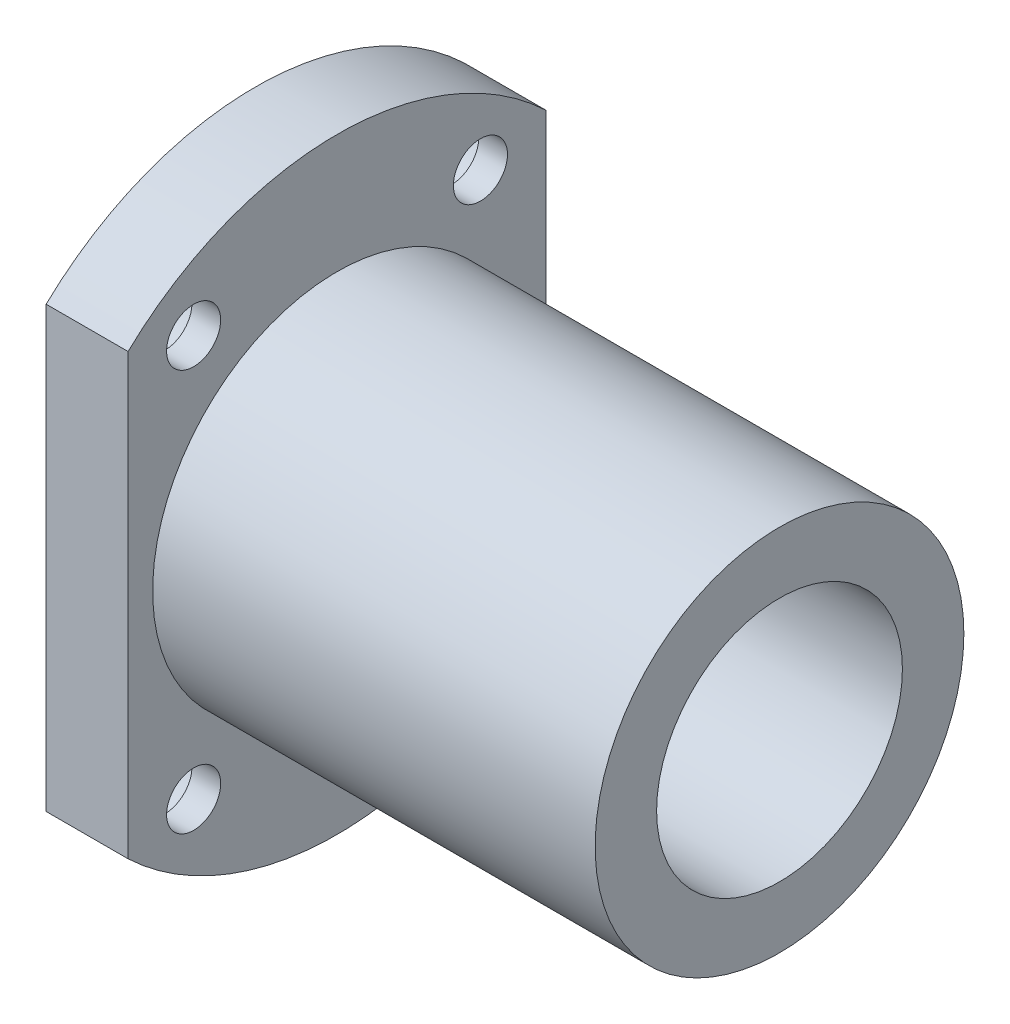
SolidWorks part; units mm, degrees
material "AISI 1045 钢，冷拔"
ref_plane "前视基准面" through (0, 0, 0) normal (0, 0, 1) x (1, 0, 0)
ref_plane "上视基准面" through (0, 0, 0) normal (0, 1, 0) x (1, 0, 0)
ref_plane "右视基准面" through (0, 0, 0) normal (1, 0, 0) x (0, 0, -1)
sketch "草图1" plane through (0, 0, 0) normal (1, 0, 0) x (0, 0, -1)
  circle A0 centre (0, 0) radius 37
  dimension "D1" = 74
extrude "凸台-拉伸1" add sketch "草图1" along normal blind 10
sketch "草图2" plane through (10, 0, 0) normal (1, 0, 0) x (0, 0, -1)
  circle A0 centre (0, 0) radius 22.5
  dimension "D1" = 45
extrude "凸台-拉伸2" add sketch "草图2" along normal blind 54
sketch "草图3" plane through (0, 0, 0) normal (-1, 0, 0) x (0, 0, 1)
  circle A0 centre (0, 0) radius 15
  dimension "D1" = 30
extrude "切除-拉伸1" cut sketch "草图3" against normal through all
sketch "草图6" plane through (0, 0, 0) normal (-1, 0, 0) x (0, 0, 1)
  line L0 (43.8334, 0) -> (-44.3546, 0) construction
  line L1 (-25.5, 26.8095) -> (-25.5, -26.8095)
  line L2 (25.5, 26.8095) -> (25.5, -26.8095)
  line L3 (0, -40.943) -> (0, 39.4328) construction
  circle A0 centre (0, 0) radius 37 construction
  arc A1 (-25.5, 26.8095) -> (-25.5, -26.8095) centre (0, 0) ccw
  arc A2 (25.5, -26.8095) -> (25.5, 26.8095) centre (0, 0) ccw
  dimension "D1" = 51
extrude "切除-拉伸2" cut sketch "草图6" against normal through all
hole_wizard "M6 六角头螺栓的柱形沉头孔2" positions "草图7" profile "草图8" counterbore size "M6" standard "GB" end condition through all
sketch "草图7" plane through (0, 0, 0) normal (-1, 0, 0) x (0, 0, 1)
  line L0 (29.5785, 0) -> (-29.4513, 0) construction
  line L3 (0, -40.0105) -> (0, 39.2472) construction
  point P0 (-17.5, 24.5)
  point P2 (17.5, 24.5)
  point P4 (17.5, -24.5)
  point P6 (-17.5, -24.5)
  point P18 (0, 0)
  dimension "D1" = 49
  dimension "D2" = 35
sketch "草图8" plane through (0, 24.5, -17.5) normal (0, 1, 0) x (0, 0, 1)
  line L0 (0, 0) -> (0, 64)
  line L1 (0, 64) -> (3.3, 64)
  line L3 (3.3, 64) -> (3.3, 6.5)
  line L4 (3.3, 6.5) -> (5.5, 6.5)
  line L5 (5.5, 6.5) -> (5.5, 0)
  line L7 (5.5, 0) -> (0, 0)
  line L11 (0, -6.35) -> (0, 107.95) construction
  dimension "通孔孔直径" = 6.6
  dimension "通孔孔深度" = 64
  dimension "柱形沉头孔直径" = 11
  dimension "柱形沉头孔深度" = 6.5
